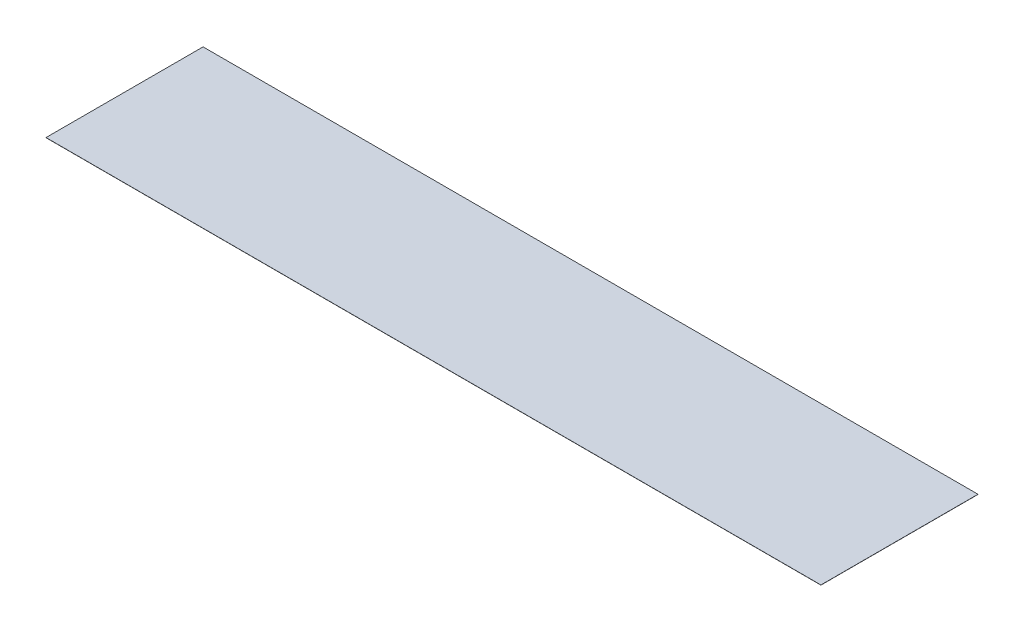
SolidWorks part; units mm, degrees
ref_plane "Front Plane" through (0, 0, 0) normal (0, 0, 1) x (1, 0, 0)
ref_plane "Top Plane" through (0, 0, 0) normal (0, 1, 0) x (1, 0, 0)
ref_plane "Right Plane" through (0, 0, 0) normal (1, 0, 0) x (0, 0, -1)
sketch "Sketch1" plane through (0, 0, 0) normal (0, 1, 0) x (1, 0, 0)
  line L1 (0, 0) -> (22555.2, 0)
  line L2 (0, 0) -> (0, 4572)
  line L3 (0, 4572) -> (22555.2, 4572)
  line L4 (22555.2, 0) -> (22555.2, 4572)
  dimension "D1" = 4572
  dimension "D2" = 22555.2
extrude "Boss-Extrude1" add sketch "Sketch1" along normal blind 4.7752
